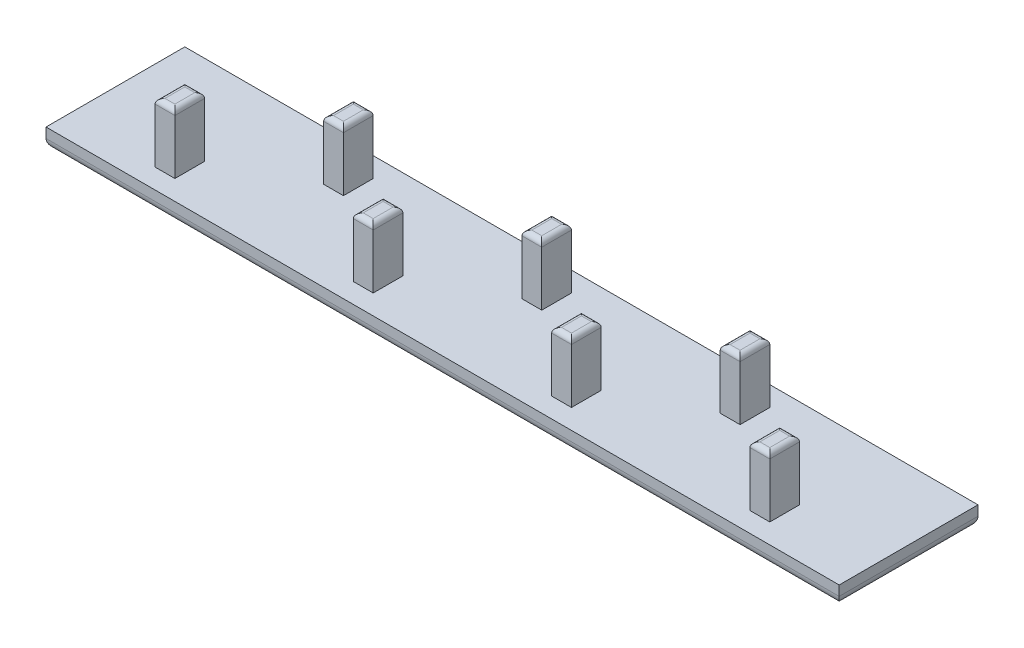
SolidWorks part; units mm, degrees
material "PVC Rigid"
ref_plane "Front Plane" through (0, 0, 0) normal (0, 0, 1) x (1, 0, 0)
ref_plane "Top Plane" through (0, 0, 0) normal (0, 1, 0) x (1, 0, 0)
ref_plane "Right Plane" through (0, 0, 0) normal (1, 0, 0) x (0, 0, -1)
sketch "Sketch1" plane through (0, 0, 0) normal (0, 1, 0) x (1, 0, 0)
  line L0 (39, 12) -> (39, 9)
  line L1 (0, 0) -> (80, 0)
  line L2 (0, 0) -> (0, 14)
  line L3 (0, 14) -> (80, 14)
  line L4 (80, 0) -> (80, 14)
  line L5 (59, 12) -> (61, 12)
  line L6 (59, 12) -> (59, 9)
  line L7 (59, 9) -> (61, 9)
  line L8 (61, 12) -> (61, 9)
  line L9 (39, 12) -> (41, 12)
  line L10 (41, 12) -> (41, 9)
  line L11 (39, 9) -> (41, 9)
  line L12 (19, 12) -> (19, 9)
  line L13 (19, 12) -> (21, 12)
  line L14 (21, 12) -> (21, 9)
  line L15 (19, 9) -> (21, 9)
  line L16 (49, 5) -> (49, 2)
  line L17 (69, 5) -> (71, 5)
  line L18 (69, 5) -> (69, 2)
  line L19 (69, 2) -> (71, 2)
  line L20 (71, 5) -> (71, 2)
  line L21 (49, 5) -> (51, 5)
  line L22 (51, 5) -> (51, 2)
  line L23 (49, 2) -> (51, 2)
  line L24 (29, 5) -> (29, 2)
  line L25 (29, 5) -> (31, 5)
  line L26 (31, 5) -> (31, 2)
  line L27 (29, 2) -> (31, 2)
  line L28 (9, 5) -> (9, 2)
  line L29 (9, 5) -> (11, 5)
  line L30 (11, 5) -> (11, 2)
  line L31 (9, 2) -> (11, 2)
  point P9 (60, 12)
  point P22 (70, 2)
  point P24 (10, 2)
  dimension "D1" = 14
  dimension "D2" = 80
  dimension "D3" = 2
  dimension "D4" = 3
  dimension "D5" = 20
  dimension "D7" = 2
  dimension "D8" = 3
  dimension "D9" = 10
  dimension "D11" = 2
  dimension "D12" = 2
  dimension "D6" = 3
  dimension "D10" = 4
extrude "Boss-Extrude1" add sketch "Sketch1" along normal blind 6 contours L12 L15 L14 L13 | L24 L27 L26 L25 | L0 L11 L10 L9 | L16 L23 L22 L21 | L8 L5 L6 L7 | L20 L17 L18 L19 | L30 L31 L28 L29
sketch "Sketch2" plane through (0, 0, 0) normal (0, -1, 0) x (1, 0, 0)
  line L1 (0, 0) -> (80, 0)
  line L2 (0, 0) -> (0, -14)
  line L3 (0, -14) -> (80, -14)
  line L4 (80, 0) -> (80, -14)
extrude "Boss-Extrude2" add sketch "Sketch2" along normal blind 2
fillet "Fillet1" radius 1 4 edges at (40, -2, 0) (80, -2, -7) (40, -2, -14) (0, -2, -7)
fillet "Fillet2" radius 0.5 28 edges at (70, 6, -2) (69, 6, -3.5) (70, 6, -5) (71, 6, -3.5) (60, 6, -9) (59, 6, -10.5) (60, 6, -12) (61, 6, -10.5) (50, 6, -5) (51, 6, -3.5) (50, 6, -2) (49, 6, -3.5) (40, 6, -12) (41, 6, -10.5) (40, 6, -9) (39, 6, -10.5) (30, 6, -5) (31, 6, -3.5) (30, 6, -2) (29, 6, -3.5) (20, 6, -12) (21, 6, -10.5) (20, 6, -9) (19, 6, -10.5) (11, 6, -3.5) (10, 6, -2) (9, 6, -3.5) (10, 6, -5)
